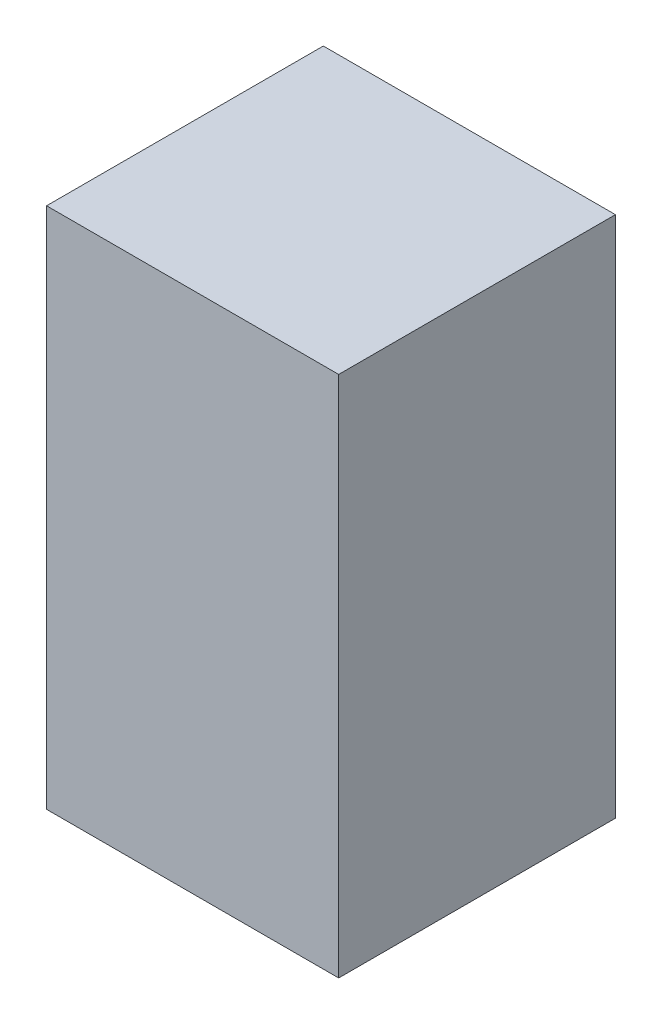
SolidWorks part; units mm, degrees
ref_plane "Płaszczyzna przednia" through (0, 0, 0) normal (0, 0, 1) x (1, 0, 0)
ref_plane "Płaszczyzna górna" through (0, 0, 0) normal (0, 1, 0) x (1, 0, 0)
ref_plane "Płaszczyzna prawa" through (0, 0, 0) normal (1, 0, 0) x (0, 0, -1)
ref_plane "Plane1" through (0, 0, 0) normal (0, 0, -1) x (-1, 0, 0)
sketch "Sketch1" plane through (0, 0, 0) normal (0, 0, -1) x (-1, 0, 0)
  line L0 (-0.475, -0.85) -> (0.475, -0.85)
  line L1 (0.475, -0.85) -> (0.475, 0.85)
  line L2 (0.475, 0.85) -> (-0.475, 0.85)
  line L3 (-0.475, 0.85) -> (-0.475, -0.85)
extrude "Boss-Extrude1" add sketch "Sketch1" against normal blind 0.9
